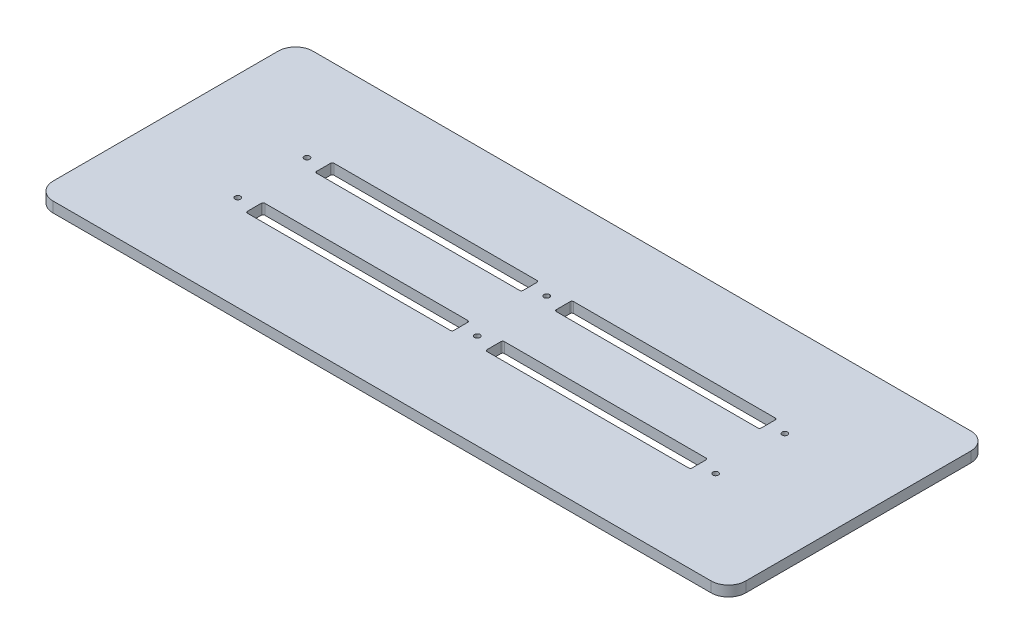
SolidWorks part; units mm, degrees
ref_plane "Ön Düzlem" through (0, 0, 0) normal (0, 0, 1) x (1, 0, 0)
ref_plane "Üst Düzlem" through (0, 0, 0) normal (0, 1, 0) x (1, 0, 0)
ref_plane "Sağ Düzlem" through (0, 0, 0) normal (1, 0, 0) x (0, 0, -1)
sketch "Çizim1" plane through (0, 0, 0) normal (0, 1, 0) x (1, 0, 0)
  line L0 (-200, 0) -> (200, 0) construction
  line L1 (-200, -75) -> (200, -75)
  line L2 (-200, -75) -> (-200, 75)
  line L3 (-200, 75) -> (200, 75)
  line L4 (200, -75) -> (200, 75)
  line L5 (-200, -75) -> (200, 75) construction
  line L6 (-200, 75) -> (200, -75) construction
  line L7 (0, 75) -> (0, -75) construction
  line L8 (127.99, -25) -> (147.19, -15) construction
  line L9 (-9.6, 15) -> (9.6, 15) construction
  line L10 (-9.6, 15) -> (-9.6, 25) construction
  line L11 (-9.6, 25) -> (9.6, 25) construction
  line L12 (9.6, 15) -> (9.6, 25) construction
  line L13 (-9.6, 15) -> (9.6, 25) construction
  line L14 (-9.6, 25) -> (9.6, 15) construction
  line L15 (127.99, 15) -> (147.19, 15) construction
  line L16 (127.99, 15) -> (127.99, 25) construction
  line L17 (127.99, 25) -> (147.19, 25) construction
  line L18 (147.19, 15) -> (147.19, 25) construction
  line L19 (127.99, 15) -> (147.19, 25) construction
  line L20 (127.99, 25) -> (147.19, 15) construction
  line L21 (-147.98, 25) -> (-128.78, 25) construction
  line L22 (-147.98, 25) -> (-147.98, 15) construction
  line L23 (-147.98, 15) -> (-128.78, 15) construction
  line L24 (-128.78, 25) -> (-128.78, 15) construction
  line L25 (-147.98, 25) -> (-128.78, 15) construction
  line L26 (-147.98, 15) -> (-128.78, 25) construction
  line L27 (127.99, -15) -> (147.19, -25) construction
  line L28 (147.19, -15) -> (147.19, -25) construction
  line L29 (127.99, -25) -> (147.19, -25) construction
  line L30 (127.99, -15) -> (127.99, -25) construction
  line L31 (127.99, -15) -> (147.19, -15) construction
  line L32 (-9.6, -25) -> (9.6, -15) construction
  line L33 (-9.6, -15) -> (9.6, -25) construction
  line L34 (9.6, -15) -> (9.6, -25) construction
  line L35 (-9.6, -25) -> (9.6, -25) construction
  line L36 (-9.6, -15) -> (-9.6, -25) construction
  line L37 (-9.6, -15) -> (9.6, -15) construction
  line L38 (-147.98, -15) -> (-128.78, -25) construction
  line L39 (-147.98, -25) -> (-128.78, -15) construction
  line L40 (-128.78, -25) -> (-128.78, -15) construction
  line L41 (-147.98, -15) -> (-128.78, -15) construction
  line L42 (-147.98, -25) -> (-147.98, -15) construction
  line L43 (-147.98, -25) -> (-128.78, -25) construction
  line L45 (-128.78, 25) -> (-9.6, 25)
  line L46 (-128.78, 25) -> (-128.78, 15)
  line L47 (-128.78, 15) -> (-9.6, 15)
  line L48 (-9.6, 25) -> (-9.6, 15)
  line L49 (9.6, 25) -> (127.99, 25)
  line L50 (9.6, 25) -> (9.6, 15)
  line L51 (9.6, 15) -> (127.99, 15)
  line L52 (127.99, 25) -> (127.99, 15)
  line L53 (9.6, -15) -> (127.99, -15)
  line L54 (9.6, -15) -> (9.6, -25)
  line L55 (9.6, -25) -> (127.99, -25)
  line L56 (127.99, -15) -> (127.99, -25)
  line L57 (-128.78, -15) -> (-9.6, -15)
  line L58 (-128.78, -15) -> (-128.78, -25)
  line L59 (-128.78, -25) -> (-9.6, -25)
  line L60 (-9.6, -15) -> (-9.6, -25)
  point P0 (0, 0)
  point P10 (0, 20)
  point P15 (137.59, 20)
  point P20 (-138.38, 20)
  point P29 (137.59, -20)
  point P34 (0, -20)
  point P39 (-138.38, -20)
  dimension "D1" = 400
  dimension "D2" = 150
  dimension "D3" = 15
  dimension "D4" = 19.2
  dimension "D5" = 10
  dimension "D6" = 137.59
  dimension "D7" = 19.2
  dimension "D8" = 138.38
  dimension "D9" = 19.2
  dimension "D10" = 118.39
  dimension "D11" = 119.18
extrude "Yükseklik-Ekstrüzyon1" add sketch "Çizim1" against normal blind 6
fillet "Radyus1" radius 10 4 edges at (200, -3, 75) (200, -3, -75) (-200, -3, -75) (-200, -3, 75)
fillet "Radyus2" radius 1 16 edges at (-128.78, -3, -15) (-128.78, -3, 25) (9.6, -3, 25) (9.6, -3, -15) (9.6, -3, 15) (9.6, -3, -25) (-128.78, -3, 15) (-9.6, -3, 15) (-9.6, -3, -25) (127.99, -3, 15) (127.99, -3, -25) (127.99, -3, -15) (127.99, -3, 25) (-9.6, -3, -15) (-9.6, -3, 25) (-128.78, -3, -25)
sketch "Çizim2" plane through (0, -6, 0) normal (0, -1, 0) x (1, 0, 0)
  line L0 (-200, 0) -> (200, 0) construction
  line L1 (-200, -65) -> (-200, 65) construction
  line L2 (200, 65) -> (200, -65) construction
  line L3 (-200, 20) -> (200, 20) construction
  line L4 (-190, 75) -> (190, 75) construction
  line L5 (0, 75) -> (0, -75) construction
  line L6 (190, -75) -> (-190, -75) construction
  circle A0 centre (-138.38, 20) radius 1.575
  circle A1 centre (-138.38, -20) radius 1.575
  circle A2 centre (0, -20) radius 1.575
  circle A3 centre (0, 20) radius 1.575
  circle A4 centre (137.59, 20) radius 1.575
  circle A5 centre (137.59, -20) radius 1.575
  point P14 (137.59, -20)
  point P15 (0, -20)
  point P16 (-138.38, -20)
  point P18 (0, 20)
  point P19 (137.59, 20)
  point P20 (-138.38, 20)
  dimension "D4" = 3.15
  dimension "D1" = 138.38
  dimension "D2" = 20
  dimension "D3" = 137.59
extrude "Kes-Ekstrüzyon1" cut sketch "Çizim2" against normal through all
